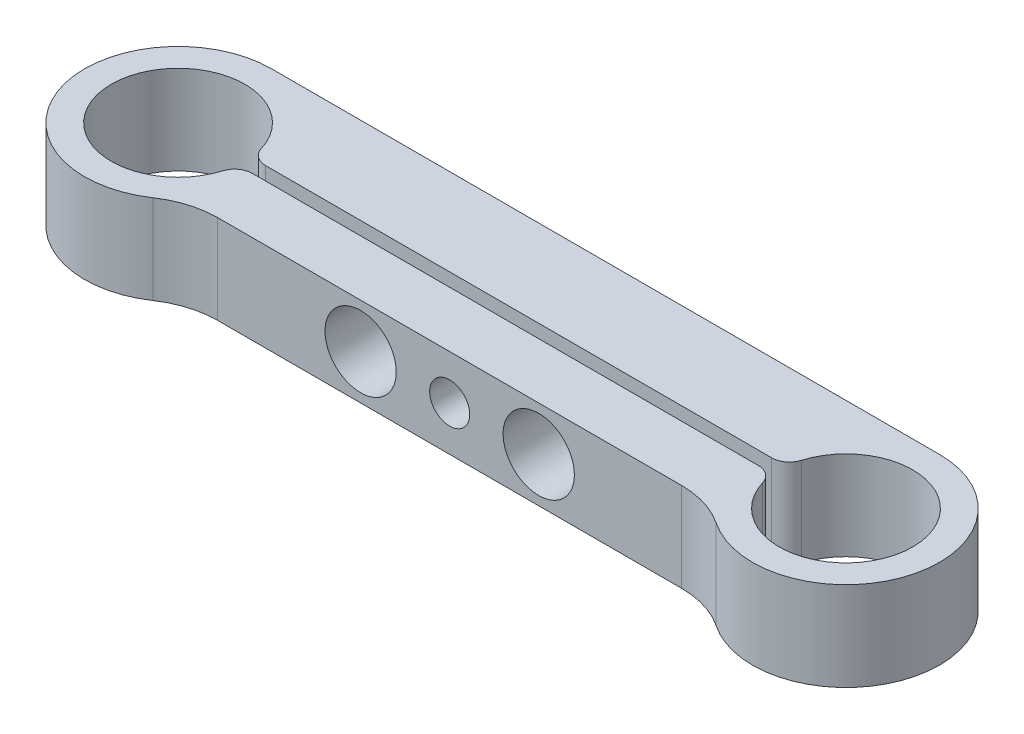
SolidWorks part; units mm, degrees
ref_plane "Спереди" through (0, 0, 0) normal (0, 0, 1) x (1, 0, 0)
ref_plane "Сверху" through (0, 0, 0) normal (0, 1, 0) x (1, 0, 0)
ref_plane "Справа" through (0, 0, 0) normal (1, 0, 0) x (0, 0, -1)
sketch "Эскиз1" plane through (0, 0, 0) normal (0, 1, 0) x (1, 0, 0)
  line L0 (0, 0) -> (75, 0) construction
  line L1 (67.1738, -7) -> (7.8262, -7)
  line L2 (0, 10.5) -> (75, 10.5)
  line L3 (7.4624, -0.75) -> (67.5376, -0.75)
  line L4 (7.4624, 0.75) -> (67.5376, 0.75)
  arc A0 (7.4624, 0.75) -> (7.4624, -0.75) centre (0, 0) ccw
  arc A1 (0, 10.5) -> (7.8262, -7) centre (0, 0) ccw
  arc A2 (67.5376, -0.75) -> (67.5376, 0.75) centre (75, 0) ccw
  arc A3 (67.1738, -7) -> (75, 10.5) centre (75, 0) ccw
  circle A5 centre (0, 0) radius 10.5 construction
  circle A6 centre (0, 0) radius 7.5 construction
  point P4 (7.1723, 2.1928)
  point P6 (10.0412, 3.0699)
  dimension "D1" = 15
  dimension "D4" = 7
  dimension "D3" = 75
  dimension "D5" = 1.5
  dimension "D2" = 3
extrude "Бобышка-Вытянуть1" add sketch "Эскиз1" along normal blind 10
sketch "Эскиз2" plane through (0, 0, 7) normal (0, 0, 1) x (1, 0, 0)
  line L0 (27.5, 5) -> (47.5, 5) construction
  line L1 (37.5, 10) -> (37.5, 0) construction
  line L2 (7.8262, 10) -> (67.1738, 10) construction
  line L3 (7.8262, 0) -> (67.1738, 0) construction
  point P8 (37.5, 5)
  dimension "D1" = 20
hole_wizard "Диаметр отверстия Ø8.0 (8)1" positions "Эскиз4" profile "Эскиз3" hole size "Ø8.0" standard "Ansi Metric" end condition up to next
sketch "Эскиз4" plane through (0, 0, 7) normal (0, 0, 1) x (1, 0, 0)
  point P0 (27.5, 5)
  point P6 (47.5, 5)
sketch "Эскиз3" plane through (27.5, 5, 7) normal (1, 0, 0) x (0, -1, 0)
  line L0 (0, 0) -> (0, 6.25)
  line L1 (0, 6.25) -> (4, 6.25)
  line L2 (4, 6.25) -> (4, 0)
  line L5 (4, 0) -> (0, 0)
  line L11 (0, -6.35) -> (0, 107.95) construction
  dimension "Диаметр сквозного отверстия" = 8
  dimension "Глубина сквозного отверстия" = 6.25
hole_wizard "Отверстие с зазором M41" positions "Эскиз6" profile "Эскиз5" hole size "M4" standard "Ansi Metric"
sketch "Эскиз6" plane through (0, 0, -0.75) normal (0, 0, 1) x (1, 0, 0)
  point P0 (47.5, 5)
  point P3 (27.5, 5)
sketch "Эскиз5" plane through (47.5, 5, -0.75) normal (1, 0, 0) x (0, -1, 0)
  line L0 (0, 0) -> (0, 12.3519)
  line L1 (0, 12.3519) -> (2.25, 11)
  line L2 (2.25, 11) -> (2.25, 0)
  line L5 (2.25, 0) -> (0, 0)
  line L10 (0, 12.3519) -> (-2.25, 11) construction
  line L11 (0, -6.35) -> (0, 107.95) construction
  dimension "Диаметр отверстия" = 4.5
  dimension "Глубина отверстия" = 11
  dimension "Угол заточки сверла" = 118
hole_wizard "Отверстие с зазором M42" positions "Эскиз8" profile "Эскиз7" hole size "M4" standard "Ansi Metric" end condition up to next
sketch "Эскиз8" plane through (0, 0, 7) normal (0, 0, 1) x (1, 0, 0)
  point P0 (37.5, 5)
sketch "Эскиз7" plane through (37.5, 5, 7) normal (1, 0, 0) x (0, -1, 0)
  line L0 (0, 0) -> (0, 6.25)
  line L1 (0, 6.25) -> (2.25, 6.25)
  line L2 (2.25, 6.25) -> (2.25, 0)
  line L5 (2.25, 0) -> (0, 0)
  line L11 (0, -6.35) -> (0, 107.95) construction
  dimension "Диаметр сквозного отверстия" = 4.5
  dimension "Глубина сквозного отверстия" = 6.25
hole_wizard "Отверстие обработанное метчиком M4x0.72" positions "Эскиз10" profile "Эскиз9" tap size "M4x0.7" standard "Ansi Metric" end condition through all
sketch "Эскиз10" plane through (0, 0, -0.75) normal (0, 0, 1) x (1, 0, 0)
  point P0 (37.5, 5)
sketch "Эскиз9" plane through (37.5, 5, -0.75) normal (1, 0, 0) x (0, -1, 0)
  line L0 (0, 0) -> (0, 9.75)
  line L1 (0, 9.75) -> (1.65, 9.75)
  line L2 (1.65, 9.75) -> (1.65, 0)
  line L5 (1.65, 0) -> (0, 0)
  line L11 (0, -6.35) -> (0, 107.95) construction
  dimension "Диаметр проходного сверла" = 3.3
  dimension "Глубина проходного сверла" = 9.75
cosmetic thread "Отверстие резьбы3" parameters "D2"=4
fillet "Скругление2" radius 10 2 edges at (7.8262, 5, 7) (67.1738, 5, 7)
fillet "Скругление3" radius 2 4 edges at (67.5376, 5, -0.75) (67.5376, 5, 0.75) (7.4624, 5, 0.75) (7.4624, 5, -0.75)
